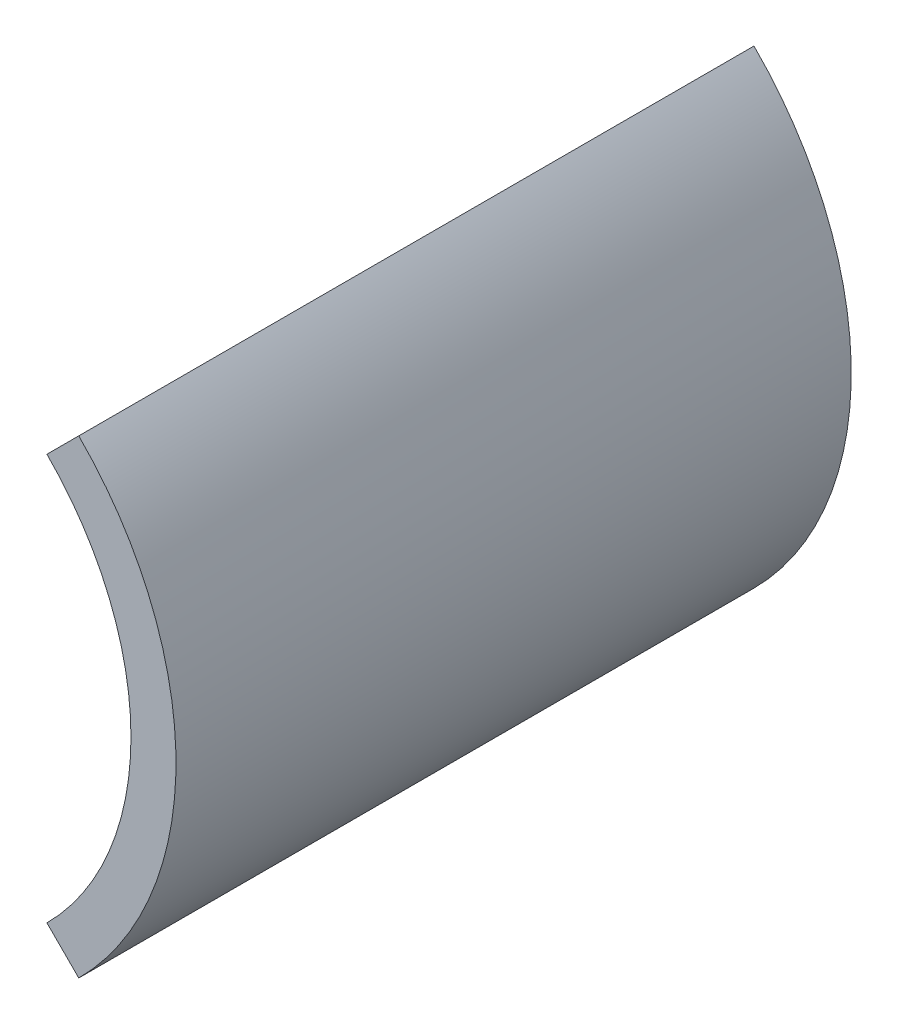
SolidWorks part; units mm, degrees
ref_plane "前视基准面" through (0, 0, 0) normal (0, 0, 1) x (1, 0, 0)
ref_plane "上视基准面" through (0, 0, 0) normal (0, 1, 0) x (1, 0, 0)
ref_plane "右视基准面" through (0, 0, 0) normal (1, 0, 0) x (0, 0, -1)
other "Configuration Table"
sketch "Sketch1" plane through (0, 0, 0) normal (0, 0, 1) x (1, 0, 0)
  line L0 (12.75, 0) -> (19.7078, 0) construction
  line L1 (9.0156, 9.0156) -> (10.4298, 10.4298)
  line L2 (9.0156, -9.0156) -> (10.4298, -10.4298)
  arc A0 (9.0156, -9.0156) -> (9.0156, 9.0156) centre (0, 0) ccw
  arc A1 (10.4298, -10.4298) -> (10.4298, 10.4298) centre (0, 0) ccw
  dimension "D1" = 29.5
  dimension "D2" = 25.5
  dimension "D3" = 90
extrude "Boss-Extrude1" add sketch "Sketch1" along normal mid plane 30
